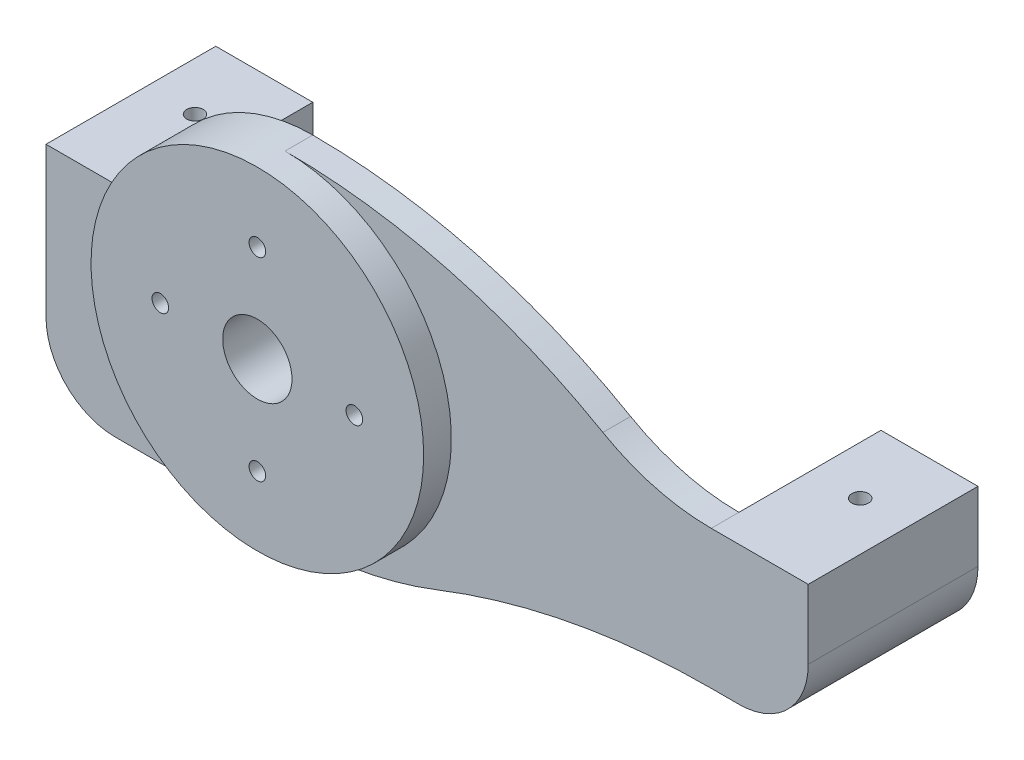
SolidWorks part; units mm, degrees
ref_plane "Alzado" through (0, 0, 0) normal (0, 0, 1) x (1, 0, 0)
ref_plane "Planta" through (0, 0, 0) normal (0, 1, 0) x (1, 0, 0)
ref_plane "Vista lateral" through (0, 0, 0) normal (1, 0, 0) x (0, 0, -1)
sketch "Croquis1" plane through (0, 0, 66.05) normal (0, 0, 1) x (1, 0, 0)
  line L0 (-13.5093, 12.5428) -> (-13.5093, -16.8346) construction
  line L1 (-8.1593, 12.5428) -> (-18.8593, 12.5428) construction
  line L2 (17.2407, 0.1428) -> (-13.5093, 8.3428) construction
  line L3 (17.2407, 0.1428) -> (17.2407, -9.8572) construction
  line L4 (17.2407, -26.6572) -> (17.2407, 7.9428) construction
  line L5 (17.2407, -9.8572) -> (-13.5093, -15.6572) construction
  line L6 (17.2407, 0.1428) -> (17.2407, -9.8572)
  line L7 (-13.5093, -15.6572) -> (-25.5093, -15.6572)
  line L8 (-25.5093, -15.6572) -> (-25.5093, -3.6572)
  arc A0 (-13.5093, 8.3428) -> (-25.5093, -3.6572) centre (-13.5093, -3.6572) ccw
  arc A1 (17.2407, -9.8572) -> (-2.5126, -13.5831) centre (17.2407, -64.0833) ccw
  arc A2 (-2.5126, -13.5831) -> (-13.5093, -15.6572) centre (-13.5093, 14.5307) cw
  arc A3 (17.2407, 0.1428) -> (9.4241, 2.2272) centre (17.2407, 15.8411) cw
  arc A4 (-13.5093, 8.3428) -> (9.4241, 2.2272) centre (-13.5093, -37.7151) cw
  dimension "D1" = 24
  dimension "D2" = 10
extrude "Saliente-Extruir1" add sketch "Croquis1" along normal blind 2
sketch "Croquis2" plane through (17.2407, 0, 0) normal (1, 0, 0) x (0, 0, -1)
  line L0 (-68.05, 0.1428) -> (-55.8, 0.1428)
  line L1 (-52.05, 0.1428) -> (-59.55, 0.1428) construction
  line L2 (-55.8, 0.1428) -> (-55.8, -9.8572)
  line L3 (-55.8, -9.8572) -> (-68.05, -9.8572)
  line L4 (-68.05, -9.8572) -> (-68.05, 0.1428)
extrude "Saliente-Extruir2" add sketch "Croquis2" along normal blind 7
fillet "Redondeo1" radius 5 1 edges at (24.2407, -9.8572, 61.925)
sketch "Croquis3" plane through (0, 0, 55.8) normal (0, 0, -1) x (-1, 0, 0)
  line L16 (-19.2407, -1.8572) -> (-22.2407, -1.8572)
  line L17 (-19.2407, -7.8572) -> (-19.2407, -1.8572)
  line L18 (-22.2407, -1.8572) -> (-22.2407, -4.8572)
  line L19 (-19.2407, -1.8572) -> (-22.2407, -1.8572)
  line L20 (-19.2407, -7.8572) -> (-19.2407, -1.8572)
  line L21 (-22.2407, -1.8572) -> (-22.2407, -4.8572)
  arc A5 (-22.2407, -4.8572) -> (-19.2407, -7.8572) centre (-19.2407, -4.8572) ccw
  arc A6 (-22.2407, -4.8572) -> (-19.2407, -7.8572) centre (-19.2407, -4.8572) ccw
  dimension "D1" = 2
extrude "Cortar-Extruir1" cut sketch "Croquis3" against normal blind 2
sketch "Croquis4" plane through (0, 0.1428, 0) normal (0, 1, 0) x (1, 0, 0)
  circle A0 centre (20.7407, -60.8) radius 0.6
  dimension "D1" = 1.2
extrude "Cortar-Extruir2" cut sketch "Croquis4" against normal blind 7
sketch "Croquis5" plane through (-23.7593, 0, 0) normal (-1, 0, 0) x (0, 0, 1)
  line L6 (55.8, 0.1428) -> (68.05, 0.1428)
  line L7 (55.8, 0.1428) -> (55.8, -15.6572)
  line L8 (55.8, -15.6572) -> (68.05, -15.6572)
  line L9 (68.05, 0.1428) -> (68.05, -15.6572)
extrude "Saliente-Extruir3" add sketch "Croquis5" along normal blind 7
fillet "Redondeo2" radius 5 1 edges at (-30.7593, -15.6572, 61.925)
sketch "Croquis6" plane through (0, 0.1428, 0) normal (0, 1, 0) x (1, 0, 0)
  circle A0 centre (-27.2593, -60.8) radius 0.6
  dimension "D1" = 1.2
extrude "Cortar-Extruir3" cut sketch "Croquis6" against normal blind 9
sketch "Croquis7" plane through (0, 0, 55.8) normal (0, 0, -1) x (-1, 0, 0)
  line L4 (25.7593, -7.8572) -> (28.7593, -7.8572)
  line L5 (30.7593, 0.1428) -> (23.7593, 0.1428) construction
  line L6 (30.7593, 0.1428) -> (30.7593, -10.6572) construction
  line L7 (23.7593, 0.1428) -> (23.7593, -15.6572) construction
  line L11 (28.7593, -7.8572) -> (28.7593, -1.8572)
  line L12 (28.7593, -1.8572) -> (25.7593, -1.8572)
  line L13 (25.7593, -1.8572) -> (25.7593, -7.8572)
  point P4 (27.2593, 0.1428)
  dimension "D2" = 8
  dimension "D1" = 2
  dimension "D3" = 2
  dimension "D4" = 2
  dimension "D5" = 6
extrude "Cortar-Extruir4" cut sketch "Croquis7" against normal blind 2
sketch "Croquis8" plane through (0, 0, 68.05) normal (0, 0, 1) x (1, 0, 0)
  line L0 (-13.5093, 12.5428) -> (-13.5093, -11.5114) construction
  line L1 (-8.1593, 12.5428) -> (-18.8593, 12.5428) construction
  circle A0 centre (-13.5093, -3.6572) radius 12
extrude "Saliente-Extruir4" add sketch "Croquis8" along normal blind 2
sketch "Croquis9" plane through (0, 0, 70.05) normal (0, 0, 1) x (1, 0, 0)
  circle A0 centre (-13.5093, -3.6572) radius 2.5
  dimension "D1" = 5
extrude "Cortar-Extruir5" cut sketch "Croquis9" against normal blind 6
sketch "Croquis10" plane through (0, 0, 70.05) normal (0, 0, 1) x (1, 0, 0)
  circle A0 centre (-13.5093, 3.3428) radius 0.6
  circle A1 centre (-6.5093, -3.6572) radius 0.6
  circle A2 centre (-13.5093, -10.6572) radius 0.6
  circle A3 centre (-20.5093, -3.6572) radius 0.6
  point P2 (-13.5093, -3.6572)
  point P13 (-13.5093, -3.6572)
  dimension "D1" = 1.2
  dimension "D2" = 7
  dimension "D3" = 4
extrude "Cortar-Extruir6" cut sketch "Croquis10" against normal blind 6
sketch "Croquis11" plane through (0, 0, 66.05) normal (0, 0, -1) x (-1, 0, 0)
  circle A0 centre (13.5093, 3.3428) radius 3
  circle A1 centre (20.5093, -3.6572) radius 3
  circle A2 centre (13.5093, -10.6572) radius 3
  circle A3 centre (6.5093, -3.6572) radius 3
  point P3 (13.5093, -3.6572)
  point P14 (13.5093, -3.6572)
  dimension "D1" = 6
  dimension "D2" = 4
extrude "Cortar-Extruir7" cut sketch "Croquis11" against normal blind 1.5
sketch "Croquis12" plane through (0, 0, 55.8) normal (0, 0, -1) x (-1, 0, 0)
  line L0 (27.2593, 0.1428) -> (27.2593, -19.2616) construction
  line L1 (30.7593, 0.1428) -> (23.7593, 0.1428) construction
  circle A0 centre (27.2593, -10.8572) radius 1.4
  dimension "D2" = 2.8
  dimension "D1" = 11
extrude "Cortar-Extruir8" cut sketch "Croquis12" against normal blind 10.5
